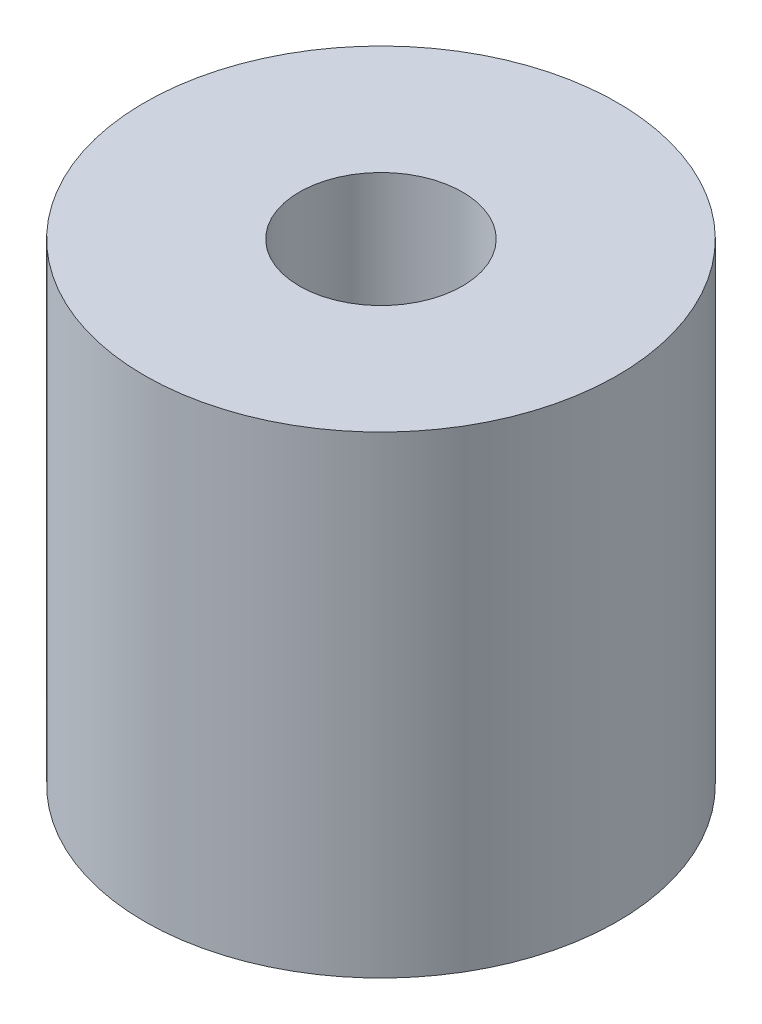
SolidWorks part; units mm, degrees
ref_plane "Front Plane" through (0, 0, 0) normal (0, 0, 1) x (1, 0, 0)
ref_plane "Top Plane" through (0, 0, 0) normal (0, 1, 0) x (1, 0, 0)
ref_plane "Right Plane" through (0, 0, 0) normal (1, 0, 0) x (0, 0, -1)
sketch "Sketch1" plane through (0, 0, 0) normal (0, 1, 0) x (1, 0, 0)
  circle A0 centre (0, 0) radius 29
  circle A1 centre (0, 0) radius 10
  dimension "D1" = 20
  dimension "D2" = 58
extrude "Boss-Extrude1" add sketch "Sketch1" along normal blind 58
